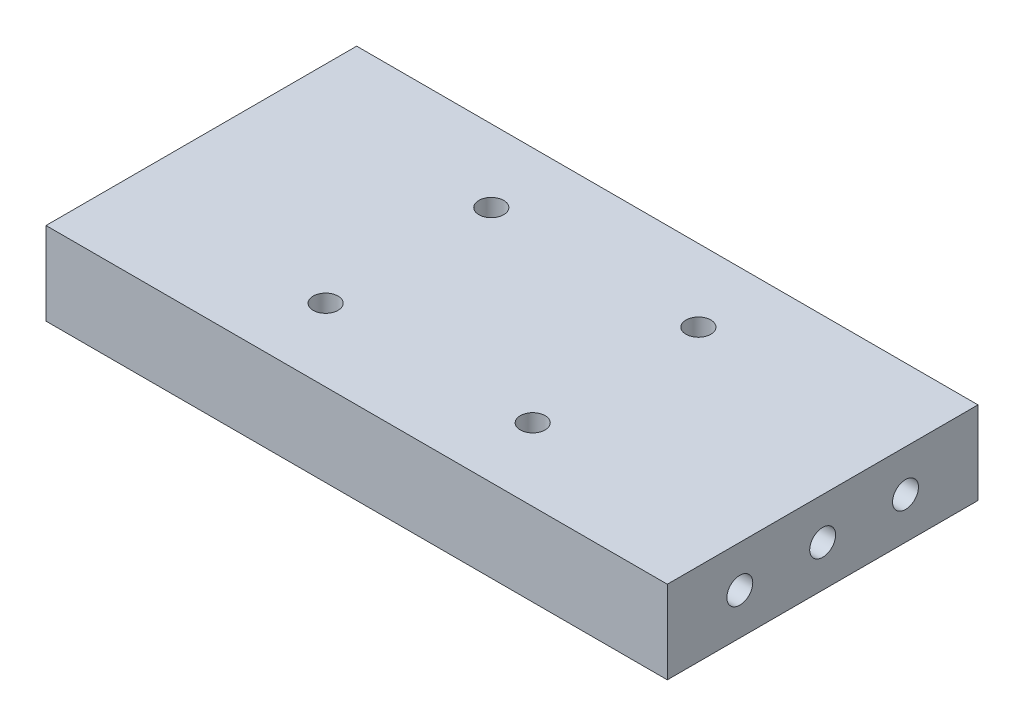
SolidWorks part; units mm, degrees
ref_plane "정면" through (0, 0, 0) normal (0, 0, 1) x (1, 0, 0)
ref_plane "윗면" through (0, 0, 0) normal (0, 1, 0) x (1, 0, 0)
ref_plane "우측면" through (0, 0, 0) normal (1, 0, 0) x (0, 0, -1)
sketch "스케치1" plane through (0, 0, 0) normal (0, 1, 0) x (1, 0, 0)
  line L1 (-30, 15) -> (30, 15)
  line L2 (-30, 15) -> (-30, -15)
  line L3 (-30, -15) -> (30, -15)
  line L4 (30, 15) -> (30, -15)
  line L5 (-30, 15) -> (30, -15) construction
  line L6 (-30, -15) -> (30, 15) construction
  point P0 (0, 0)
  dimension "D1" = 60
  dimension "D2" = 30
extrude "보스-돌출1" add sketch "스케치1" along normal blind 8
sketch "스케치2" plane through (0, 8, 0) normal (0, 1, 0) x (1, 0, 0)
  line L0 (0, 0) -> (0, 50000) construction
  line L1 (0, 0) -> (50000, 0) construction
  circle A0 centre (-10, 8) radius 1.2
  circle A1 centre (10, 8) radius 1.2
  circle A2 centre (10, -8) radius 1.2
  circle A3 centre (-10, -8) radius 1.2
  dimension "D1" = 2.4
  dimension "D2" = 10
  dimension "D3" = 8
extrude "컷-돌출1" cut sketch "스케치2" against normal up to next
sketch "스케치3" plane through (-30, 0, 0) normal (-1, 0, 0) x (0, 0, 1)
  line L0 (0, 0) -> (0, 50000) construction
  line L1 (0, 4) -> (50000, 4) construction
  line L2 (-15, 0) -> (15, 0) construction
  circle A0 centre (0, 4) radius 1.5
  circle A1 centre (-8, 4) radius 1.5
  circle A2 centre (8, 4) radius 1.5
  dimension "D2" = 3
  dimension "D3" = 3
  dimension "D4" = 3
  dimension "D1" = 4
  dimension "D5" = 8
  dimension "D6" = 8
sketch "스케치7" plane through (30, 0, 0) normal (1, 0, 0) x (0, 0, -1)
  line L0 (0, 0) -> (0, 50000) construction
  line L1 (0, 4) -> (50000, 4) construction
  line L2 (-15, 0) -> (15, 0) construction
  circle A0 centre (0, 4) radius 1.5
  circle A1 centre (-8, 4) radius 1.5
  circle A2 centre (8, 4) radius 1.5
  dimension "D2" = 3
  dimension "D3" = 3
  dimension "D4" = 3
  dimension "D1" = 4
  dimension "D5" = 8
  dimension "D6" = 8
hole_wizard "M3 나사 구멍1" positions "스케치8" profile "스케치9" tap size "M3" standard "ISO"
sketch "스케치8" plane through (-30, 0, 0) normal (-1, 0, 0) x (0, 0, 1)
  point P0 (-8, 4)
  point P3 (0, 4)
  point P6 (8, 4)
sketch "스케치9" plane through (-30, 4, -8) normal (0, 1, 0) x (0, 0, 1)
  line L0 (0, 0) -> (0, 9.2511)
  line L1 (0, 9.2511) -> (1.25, 8.5)
  line L2 (1.25, 8.5) -> (1.25, 0)
  line L5 (1.25, 0) -> (0, 0)
  line L10 (0, 9.2511) -> (-1.25, 8.5) construction
  line L11 (0, -6.35) -> (0, 107.95) construction
  dimension "탭 드릴 지름" = 2.5
  dimension "탭 드릴 깊이" = 8.5
  dimension "드릴 각도" = 118
cosmetic thread "구멍 나사산1"
cosmetic thread "구멍 나사산2"
cosmetic thread "구멍 나사산3"
hole_wizard "M3 나사 구멍2" positions "스케치10" profile "스케치11" tap size "M3" standard "ISO"
sketch "스케치10" plane through (30, 0, 0) normal (1, 0, 0) x (0, 0, -1)
  point P0 (-8, 4)
  point P3 (0, 4)
  point P6 (8, 4)
sketch "스케치11" plane through (30, 4, 8) normal (0, 1, 0) x (0, 0, -1)
  line L0 (0, 0) -> (0, 9.2511)
  line L1 (0, 9.2511) -> (1.25, 8.5)
  line L2 (1.25, 8.5) -> (1.25, 0)
  line L5 (1.25, 0) -> (0, 0)
  line L10 (0, 9.2511) -> (-1.25, 8.5) construction
  line L11 (0, -6.35) -> (0, 107.95) construction
  dimension "탭 드릴 지름" = 2.5
  dimension "탭 드릴 깊이" = 8.5
  dimension "드릴 각도" = 118
cosmetic thread "구멍 나사산4"
cosmetic thread "구멍 나사산5"
cosmetic thread "구멍 나사산6"
